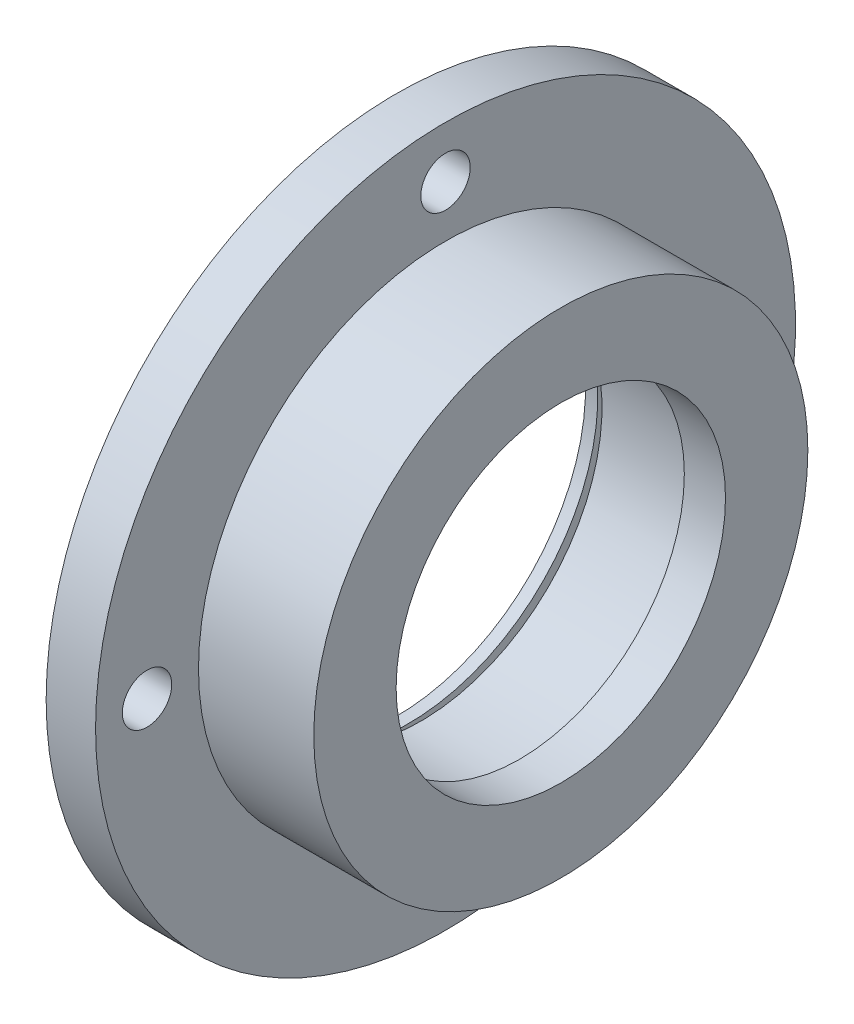
SolidWorks part; units mm, degrees
ref_plane "Plano frontal" through (0, 0, 0) normal (0, 0, 1) x (1, 0, 0)
ref_plane "Plano superior" through (0, 0, 0) normal (0, 1, 0) x (1, 0, 0)
ref_plane "Plano direito" through (0, 0, 0) normal (1, 0, 0) x (0, 0, -1)
sketch "Esboço1" plane through (0, 0, 0) normal (0, 0, 1) x (1, 0, 0)
  line L0 (0, 0) -> (0, 110.9096) construction
  line L1 (0, 0) -> (113.3933, 0) construction
  line L2 (0, 23) -> (0, 42.5)
  line L3 (0, 42.5) -> (6, 42.5)
  line L4 (6, 42.5) -> (6, 30)
  line L5 (6, 30) -> (20, 30)
  line L6 (20, 30) -> (20, 20)
  line L7 (20, 20) -> (15, 20)
  line L8 (15, 20) -> (15, 22)
  line L9 (15, 22) -> (3, 22)
  line L10 (3, 22) -> (3, 24.5)
  line L11 (3, 24.5) -> (1.5, 24.5)
  line L12 (1.5, 24.5) -> (1.5, 23)
  line L13 (1.5, 23) -> (0, 23)
  dimension "D1" = 12
  dimension "D2" = 40
  dimension "D3" = 85
  dimension "D4" = 60
  dimension "D5" = 1.5
  dimension "D6" = 1.5
  dimension "D7" = 46
  dimension "D8" = 44
  dimension "D9" = 6
  dimension "D10" = 5
  dimension "D11" = 20
revolve "Revolução1" add sketch "Esboço1" angle 360 about L1
sketch "Esboço2" plane through (6, 0, 0) normal (1, 0, 0) x (0, 0, -1)
  line L0 (0, 30) -> (0, 42.5) construction
  circle A0 centre (0, 0) radius 36.25 construction
  circle A1 centre (0, 36.25) radius 3
  circle A2 centre (36.25, 0) radius 3
  circle A3 centre (0, -36.25) radius 3
  circle A4 centre (-36.25, 0) radius 3
  circle A5 centre (0, 0) radius 30 construction
  circle A6 centre (0, 0) radius 42.5 construction
  point P14 (0, 0)
  point P19 (0, 36.25)
  dimension "D2" = 6
  dimension "D3" = 4
extrude "Corte-extrusão1" cut sketch "Esboço2" against normal through all
